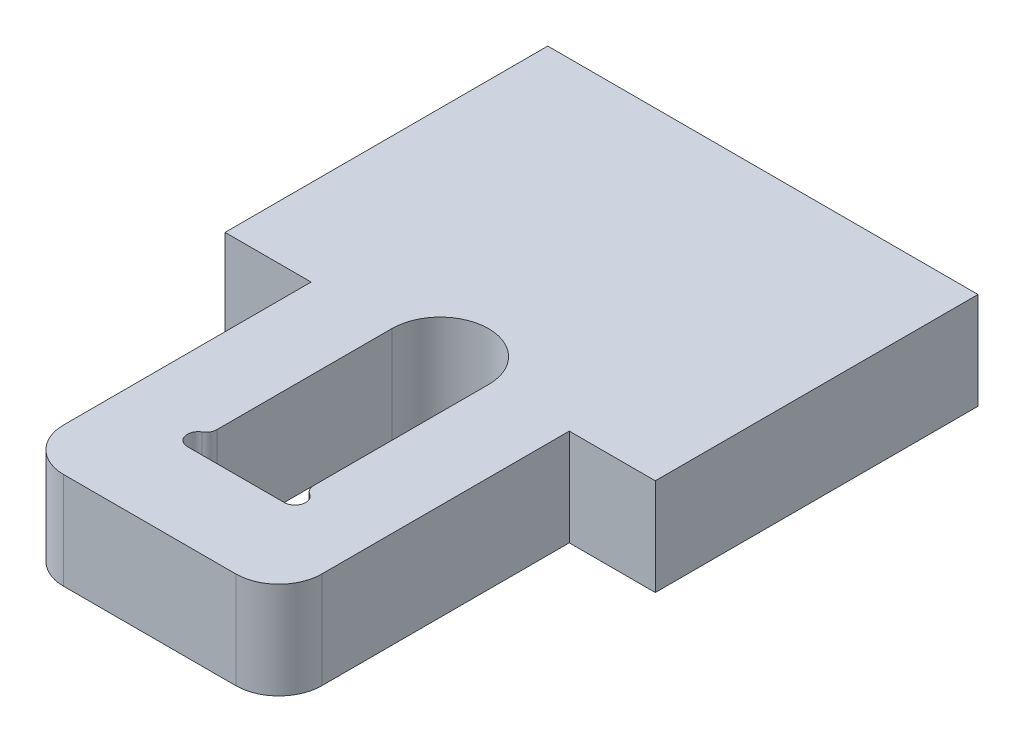
SolidWorks part; units mm, degrees
ref_plane "Front Plane" through (0, 0, 0) normal (0, 0, 1) x (1, 0, 0)
ref_plane "Top Plane" through (0, 0, 0) normal (0, 1, 0) x (1, 0, 0)
ref_plane "Right Plane" through (0, 0, 0) normal (1, 0, 0) x (0, 0, -1)
sketch "Sketch1" plane through (0, 0, 0) normal (0, 1, 0) x (1, 0, 0)
  line L0 (-10, 0) -> (-10, 15)
  line L1 (6, 0) -> (10, 0)
  line L2 (10, 0) -> (10, 15)
  line L3 (-6, 0) -> (-10, 0)
  line L4 (2.25, 0) -> (2.25, -8.134)
  line L5 (-6, 0) -> (-6, -11.5)
  line L6 (-4, -13.5) -> (4, -13.5)
  line L7 (6, -11.5) -> (6, 0)
  line L8 (-2.25, 0) -> (-2.25, -8.134)
  line L9 (-10, 15) -> (10, 15)
  line L10 (0, 15) -> (0, -13.5) construction
  line L11 (-10.8671, 0) -> (11.6584, 0) construction
  line L14 (-2.25, -9.5) -> (2.25, -9.5)
  line L16 (-2.25, 0) -> (2.25, -9.5) construction
  line L17 (-2.25, -9.5) -> (2.25, 0) construction
  arc A0 (-2.25, 0) -> (2.25, 0) centre (0, 0) cw
  arc A3 (4, -13.5) -> (6, -11.5) centre (4, -11.5) ccw
  arc A4 (-4, -13.5) -> (-6, -11.5) centre (-4, -11.5) cw
  arc A8 (2.25, -9.5) -> (2.5, -8.567) centre (2.25, -9) ccw
  arc A9 (2.5, -8.567) -> (2.25, -8.134) centre (2.75, -8.134) cw
  arc A10 (-2.25, -9.5) -> (-2.5, -8.567) centre (-2.25, -9) cw
  arc A11 (-2.5, -8.567) -> (-2.25, -8.134) centre (-2.75, -8.134) ccw
  point P19 (0, -4.75)
  dimension "D1" = 12
  dimension "D3" = 4
  dimension "D4" = 2
  dimension "D8" = 0.5
  dimension "D2" = 15
  dimension "D5" = 4
  dimension "D7" = 9.5
  dimension "D9" = 4.5
extrude "Boss-Extrude1" add sketch "Sketch1" along normal blind 4.5
